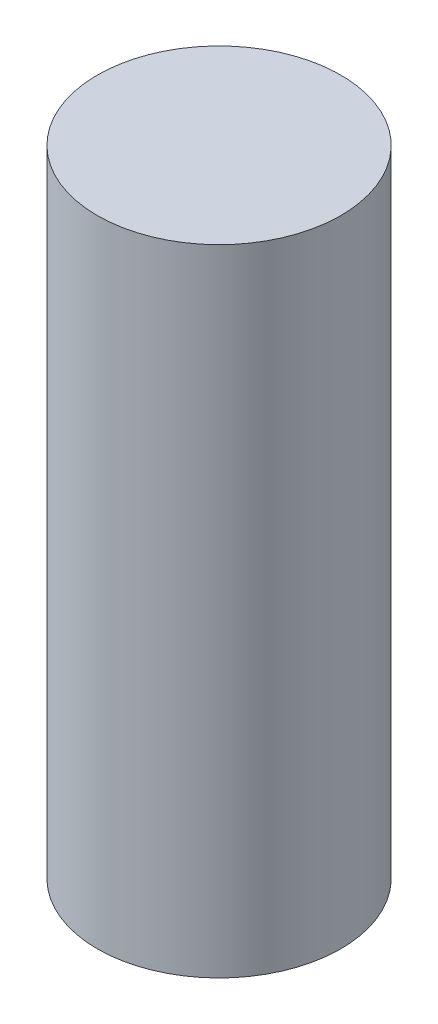
SolidWorks part; units mm, degrees
ref_plane "Front Plane" through (0, 0, 0) normal (0, 0, 1) x (1, 0, 0)
ref_plane "Top Plane" through (0, 0, 0) normal (0, 1, 0) x (1, 0, 0)
ref_plane "Right Plane" through (0, 0, 0) normal (1, 0, 0) x (0, 0, -1)
sketch "Sketch1" plane through (0, 0, 0) normal (0, 1, 0) x (1, 0, 0)
  circle A0 centre (0, 0) radius 2.875
  dimension "D1" = 5.75
extrude "Boss-Extrude1" add sketch "Sketch1" along normal blind 15
